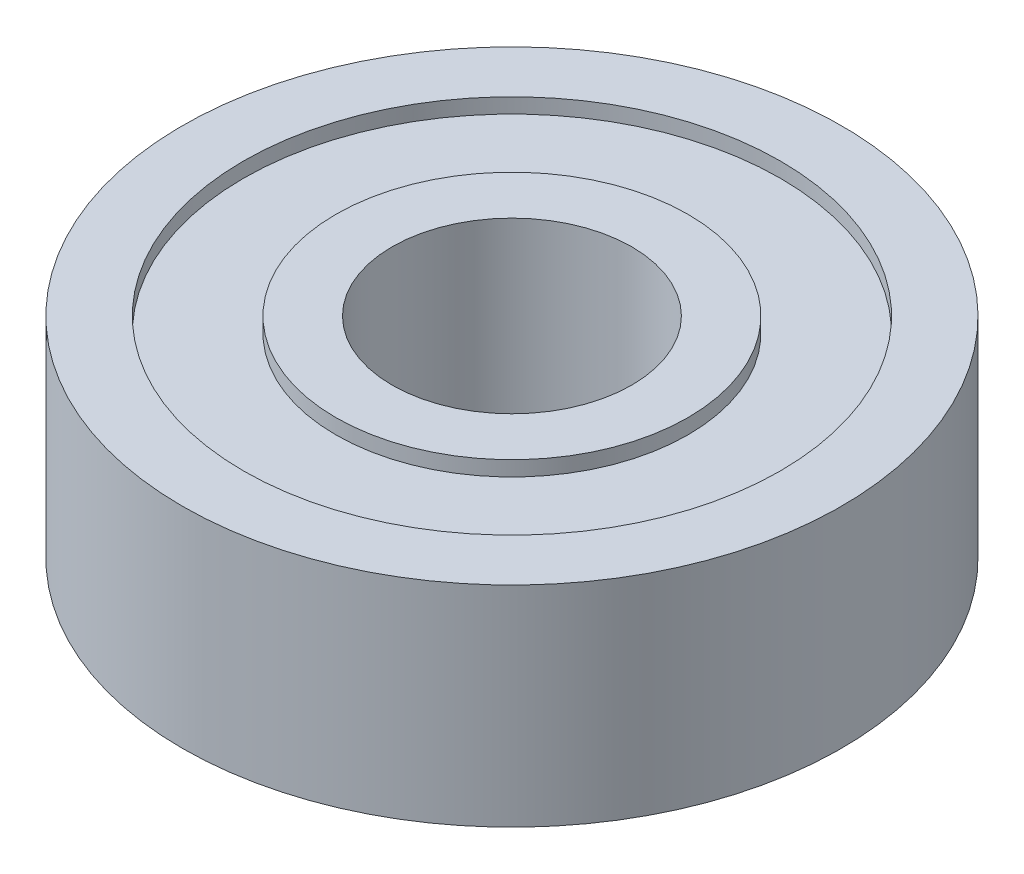
SolidWorks part; units mm, degrees
ref_plane "Plan de face" through (0, 0, 0) normal (0, 0, 1) x (1, 0, 0)
ref_plane "Plan de dessus" through (0, 0, 0) normal (0, 1, 0) x (1, 0, 0)
ref_plane "Plan de droite" through (0, 0, 0) normal (1, 0, 0) x (0, 0, -1)
sketch "Esquisse1" plane through (0, 0, 0) normal (0, 1, 0) x (1, 0, 0)
  circle A0 centre (0, 0) radius 4
  circle A1 centre (0, 0) radius 11
  dimension "D1" = 8
  dimension "D2" = 22
extrude "Boss.-Extru.1" add sketch "Esquisse1" along normal blind 7
sketch "Esquisse2" plane through (0, 7, 0) normal (0, 1, 0) x (1, 0, 0)
  circle A0 centre (0, 0) radius 5.8766
  circle A1 centre (0, 0) radius 8.9597
extrude "Enlèv. mat.-Extru.1" cut sketch "Esquisse2" against normal blind 0.5
ref_plane "Plan1" through (0, 3.5, 0) normal (0, 1, 0) x (1, 0, 0)
mirror "Symétrie1" about plane through (0, 3.5, 0) normal (0, 1, 0) of "Enlèv. mat.-Extru.1"
